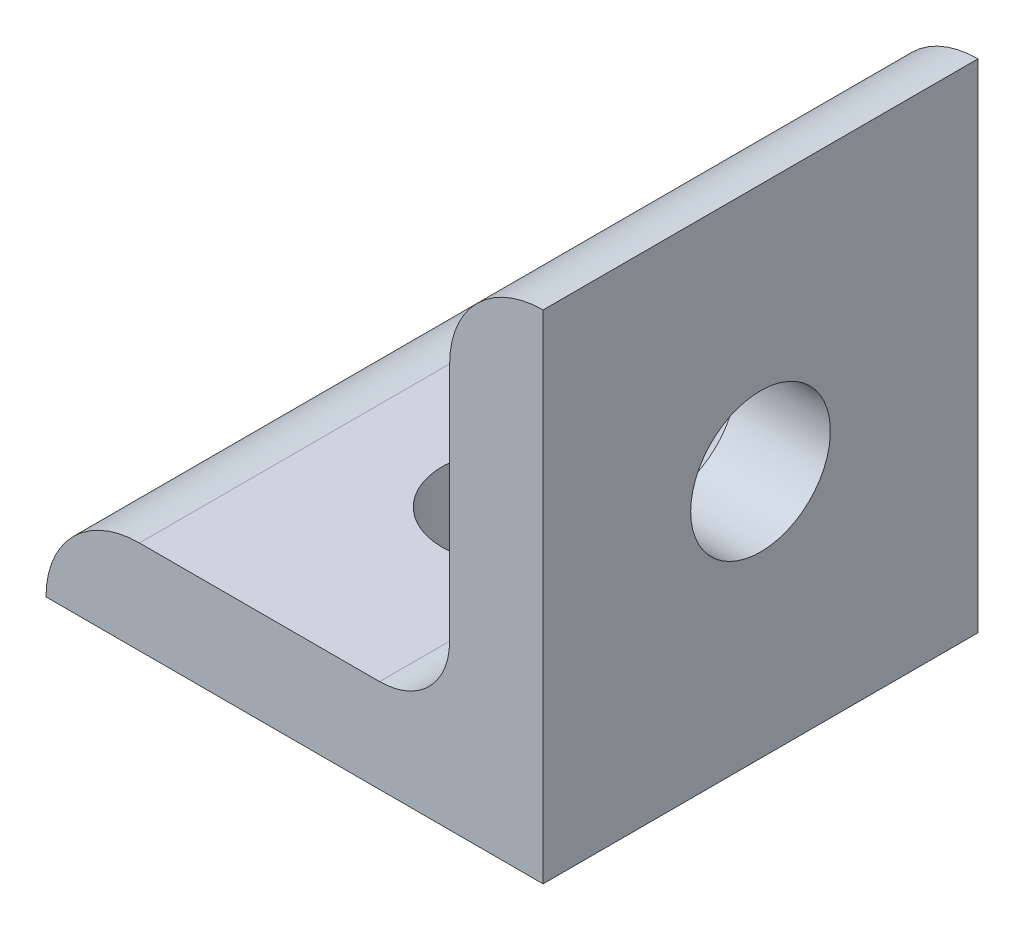
SolidWorks part; units mm, degrees
ref_plane "Front Plane" through (0, 0, 0) normal (0, 0, 1) x (1, 0, 0)
ref_plane "Top Plane" through (0, 0, 0) normal (0, 1, 0) x (1, 0, 0)
ref_plane "Right Plane" through (0, 0, 0) normal (1, 0, 0) x (0, 0, -1)
sketch "Sketch1" plane through (0, 0, 0) normal (0, 0, 1) x (1, 0, 0)
  line L0 (0, 0) -> (0, 25.4)
  line L1 (0, 0) -> (-25.4, 0)
  line L2 (-20.6248, 4.7752) -> (-8.3566, 4.7752)
  line L3 (-4.7752, 8.3566) -> (-4.7752, 20.6248)
  line L4 (-12.7, 0) -> (-12.7, 4.7752) construction
  line L5 (-4.7752, 12.7) -> (0, 12.7) construction
  arc A0 (-25.4, 0) -> (-20.6248, 4.7752) centre (-20.6248, 0) cw
  arc A1 (-4.7752, 20.6248) -> (0, 25.4) centre (0, 20.6248) cw
  arc A2 (-8.3566, 4.7752) -> (-4.7752, 8.3566) centre (-8.3566, 8.3566) ccw
  point P11 (-12.7, 4.7752)
  point P12 (-4.7752, 12.7)
  dimension "D1" = 4.7752
  dimension "D3" = 3.5814
  dimension "D" = 4.7752
  dimension "D2" = 4.7752
  dimension "B" = 25.4
  dimension "C" = 25.4
extrude "Extrude1" add sketch "Sketch1" against normal mid plane 22.225
sketch "Sketch2" plane through (0, 4.7752, 0) normal (0, 1, 0) x (1, 0, 0)
  circle A0 centre (-12.7, 0) radius 3.5687
  dimension "hole" = 7.1374
extrude "Cut-Extrude1" cut sketch "Sketch2" against normal through all
sketch "Sketch3" plane through (-4.7752, 0, 0) normal (-1, 0, 0) x (0, 0, 1)
  circle A0 centre (0, 12.7) radius 3.5687
  dimension "D1" = 7.1374
extrude "Cut-Extrude2" cut sketch "Sketch3" against normal through all
sketch "Sketch4" [suppressed] plane through (0, 6.35, 0) normal (0, 1, 0) x (1, 0, 0)
  line L0 (-69.85, 0) -> (-39.8907, 0) construction
  line L1 (-39.8907, 0) -> (-9.9314, 0) construction
  circle A0 centre (-24.911, 0) radius 4.1656
  circle A1 centre (-54.8703, 0) radius 4.1656
  dimension "D1" = 7.1374
extrude "Cut-Extrude3" [suppressed] cut sketch "Sketch4" against normal through all
sketch "Sketch5" [suppressed] plane through (-6.35, 0, 0) normal (-1, 0, 0) x (0, 0, 1)
  line L0 (0, 9.9314) -> (0, 39.8907) construction
  line L1 (0, 39.8907) -> (0, 69.85) construction
  circle A0 centre (0, 54.8703) radius 4.1656
  circle A1 centre (0, 24.911) radius 4.1656
  dimension "D1" = 7.1374
extrude "Cut-Extrude4" [suppressed] cut sketch "Sketch5" against normal through all
sketch "Sketch6" [suppressed] plane through (0, 6.35, 0) normal (0, 1, 0) x (1, 0, 0)
  line L0 (-20.8407, 23.2156) -> (-20.8407, 35.687) construction
  line L1 (-9.9314, 35.687) -> (-31.75, 35.687) construction
  line L2 (-20.8407, -23.2156) -> (-20.8407, -35.687) construction
  line L3 (-9.9314, -35.687) -> (-31.75, -35.687) construction
  circle A0 centre (-20.8407, 19.05) radius 4.1656
  circle A1 centre (-20.8407, -19.05) radius 4.1656
  dimension "D1" = 7.1374
  dimension "distance" = 25.4
extrude "Cut-Extrude5" [suppressed] cut sketch "Sketch6" against normal through all
sketch "Sketch7" [suppressed] plane through (-6.35, 0, 0) normal (-1, 0, 0) x (0, 0, 1)
  line L0 (23.2156, 20.8407) -> (35.687, 20.8407) construction
  line L1 (35.687, 31.75) -> (35.687, 9.9314) construction
  line L2 (-23.2156, 20.8407) -> (-35.687, 20.8407) construction
  line L3 (-35.687, 31.75) -> (-35.687, 9.9314) construction
  circle A0 centre (-19.05, 20.8407) radius 4.1656
  circle A1 centre (19.05, 20.8407) radius 4.1656
  dimension "D2" = 7.1374
  dimension "D1" = 25.4
extrude "Cut-Extrude6" [suppressed] cut sketch "Sketch7" against normal through all
sketch "Sketch8" [suppressed] plane through (0, 4.7752, 0) normal (0, 1, 0) x (1, 0, 0)
  line L0 (-46.0248, 0) -> (-27.1907, 0) construction
  line L1 (-27.1907, 0) -> (-8.3566, 0) construction
  line L2 (-17.7737, 0) -> (-17.7737, -12.7) construction
  line L3 (-36.6078, 0) -> (-36.6078, -12.7) construction
  circle A0 centre (-36.6078, -12.7) radius 3.5687
  circle A1 centre (-17.7737, -12.7) radius 3.5687
  circle A2 centre (-17.7737, 12.7) radius 3.5687
  circle A3 centre (-36.6078, 12.7) radius 3.5687
  dimension "D1" = 7.1374
  dimension "distance" = 42.6089
extrude "Cut-Extrude7" [suppressed] cut sketch "Sketch8" against normal through all
sketch "Sketch9" [suppressed] plane through (-4.7752, 0, 0) normal (-1, 0, 0) x (0, 0, 1)
  line L0 (0, 8.3566) -> (0, 27.1907) construction
  line L1 (0, 27.1907) -> (0, 46.0248) construction
  line L2 (0, 36.6078) -> (12.7, 36.6078) construction
  line L3 (0, 17.7737) -> (12.7, 17.7737) construction
  circle A0 centre (12.7, 17.7737) radius 3.5687
  circle A1 centre (12.7, 36.6078) radius 3.5687
  circle A2 centre (-12.7, 17.7737) radius 3.5687
  circle A3 centre (-12.7, 36.6078) radius 3.5687
  dimension "D1" = 7.1374
  dimension "D2" = 42.6089
extrude "Cut-Extrude8" [suppressed] cut sketch "Sketch9" against normal through all
equation "\"D2@Sketch1\" = \"D@Sketch1\""
equation "\"D3@Sketch1\" = \"D1@Sketch1\"*.750"
equation "\"D1@Sketch3\" = \"hole@Sketch2\""
equation "\"D1@Sketch4\" = \"hole@Sketch2\""
equation "\"D1@Sketch5\" = \"hole@Sketch2\""
equation "\"D1@Sketch6\" = \"hole@Sketch2\""
equation "\"D2@Sketch7\" = \"hole@Sketch2\""
equation "\"D1@Sketch7\" = \"distance@Sketch6\""
equation "\"D1@Sketch8\" = \"hole@Sketch2\""
equation "\"D1@Sketch9\" = \"hole@Sketch2\""
equation "\"D2@Sketch9\" = \"distance@Sketch8\""
